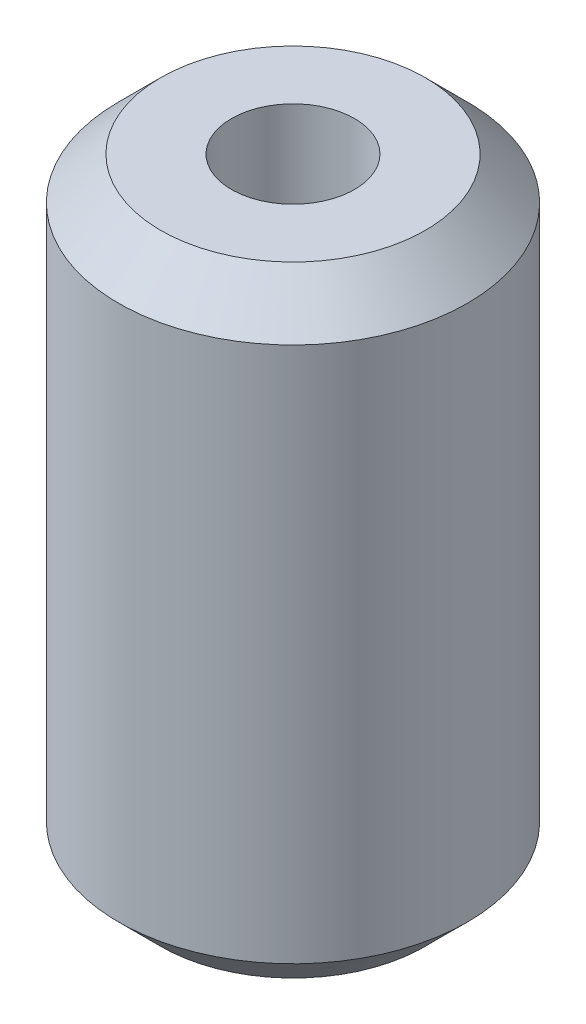
SolidWorks part; units mm, degrees
material "Fonte ductile"
ref_plane "Plan de face" through (0, 0, 0) normal (0, 0, 1) x (1, 0, 0)
ref_plane "Plan de dessus" through (0, 0, 0) normal (0, 1, 0) x (1, 0, 0)
ref_plane "Plan de droite" through (0, 0, 0) normal (1, 0, 0) x (0, 0, -1)
sketch "Esquisse1" plane through (0, 0, 0) normal (0, 0, 1) x (1, 0, 0)
  line L0 (0, 16.543) -> (0, -16.543) construction
  line L1 (-3.175, -15.457) -> (-6.8277, -15.457)
  line L2 (-6.8277, -15.457) -> (-9, -13.2847)
  line L3 (-9, -13.2847) -> (-9, 14.3706)
  line L4 (-9, 14.3706) -> (-6.8277, 16.543)
  line L5 (-6.8277, 16.543) -> (-3.175, 16.543)
  line L6 (-3.175, 16.543) -> (-3.175, -15.457)
  dimension "D1" = 32
  dimension "D2" = 135
  dimension "D3" = 3.175
  dimension "D4" = 18
revolve "Révolution1" add sketch "Esquisse1" angle 360 about L0
